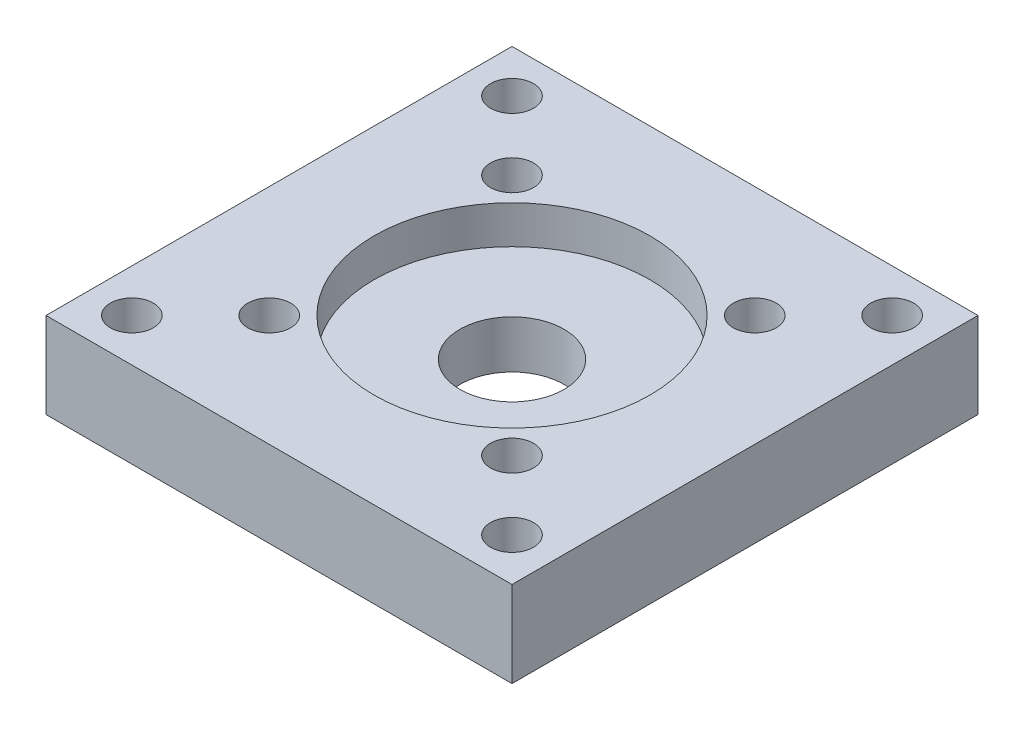
SolidWorks part; units mm, degrees
ref_plane "Front Plane" through (0, 0, 0) normal (0, 0, 1) x (1, 0, 0)
ref_plane "Top Plane" through (0, 0, 0) normal (0, 1, 0) x (1, 0, 0)
ref_plane "Right Plane" through (0, 0, 0) normal (1, 0, 0) x (0, 0, -1)
sketch "Sketch1" plane through (0, 0, 0) normal (0, 1, 0) x (1, 0, 0)
  line L1 (-19, -19) -> (19, -19)
  line L2 (-19, -19) -> (-19, 19)
  line L3 (-19, 19) -> (19, 19)
  line L4 (19, -19) -> (19, 19)
  line L5 (-19, -19) -> (19, 19) construction
  line L6 (-19, 19) -> (19, -19) construction
  point P0 (0, 0)
  dimension "D1" = 38
  dimension "D2" = 38
extrude "Boss-Extrude1" add sketch "Sketch1" along normal blind 7
sketch "Sketch2" plane through (0, 7, 0) normal (0, 1, 0) x (1, 0, 0)
  line L1 (15.5, -15.5) -> (-15.5, -15.5)
  line L2 (15.5, -15.5) -> (15.5, 15.5)
  line L3 (15.5, 15.5) -> (-15.5, 15.5)
  line L4 (-15.5, -15.5) -> (-15.5, 15.5)
  line L5 (15.5, -15.5) -> (-15.5, 15.5) construction
  line L6 (15.5, 15.5) -> (-15.5, -15.5) construction
  circle A0 centre (-15.5, 15.5) radius 1.75
  circle A1 centre (15.5, 15.5) radius 1.75
  circle A2 centre (15.5, -15.5) radius 1.75
  circle A3 centre (-15.5, -15.5) radius 1.75
  circle A4 centre (0, 0) radius 4.25
  point P0 (0, 0)
  dimension "D1" = 31
  dimension "D2" = 31
extrude "Cut-Extrude1" cut sketch "Sketch2" against normal blind 7 contours L3 A0 L4 | L4 A0 L3 | L2 A1 L3 | L1 A2 L2 | L4 A3 L1 | L1 A3 L4 | L2 A2 L1 | L3 A1 L2 | A4
sketch "Sketch3" plane through (0, 7, 0) normal (0, 1, 0) x (1, 0, 0)
  circle A0 centre (0, 0) radius 11.25
extrude "Cut-Extrude2" cut sketch "Sketch3" against normal blind 3.1
sketch "Sketch5" plane through (0, 7, 0) normal (0, 1, 0) x (1, 0, 0)
  line L0 (0, 0) -> (0, 5.6428)
  line L1 (0, 0) -> (-2.0053, 0)
  line L2 (0, 0) -> (2.938, 0)
  line L3 (0, 0) -> (0, -2.0986)
  line L4 (0, 0) -> (-9.8995, 9.8995)
  line L5 (0, 0) -> (9.8995, 9.8995)
  line L6 (0, 0) -> (-9.8995, -9.8995)
  line L7 (0, 0) -> (9.8995, -9.8995)
  circle A0 centre (0, 0) radius 14
  circle A1 centre (-9.8995, 9.8995) radius 1.75
  circle A2 centre (9.8995, 9.8995) radius 1.75
  circle A3 centre (9.8995, -9.8995) radius 1.75
  circle A4 centre (-9.8995, -9.8995) radius 1.75
extrude "Cut-Extrude3" cut sketch "Sketch5" against normal blind 27 contours A0 A1 | A0 A1 L4 | L4 A1 A0 | A0 A4 | A0 A3 | A0 A2 | A0 A2 L5 | L5 A2 A0 | L7 A3 A0 | A0 A3 L7 | L6 A4 A0 | A0 A4 L6
sketch "Sketch6" plane through (0, 0, 0) normal (0, -1, 0) x (1, 0, 0)
  circle A0 centre (-9.8995, 9.8995) radius 2.75
  circle A1 centre (9.8995, 9.8995) radius 2.75
  circle A2 centre (9.8995, -9.8995) radius 2.75
  circle A3 centre (-9.8995, -9.8995) radius 2.75
  circle A4 centre (-9.8995, 9.8995) radius 1.75
  circle A5 centre (9.8995, 9.8995) radius 1.75
  circle A6 centre (9.8995, -9.8995) radius 1.75
  circle A7 centre (-9.8995, -9.8995) radius 1.75
extrude "Cut-Extrude14" cut sketch "Sketch6" against normal blind 3.5
